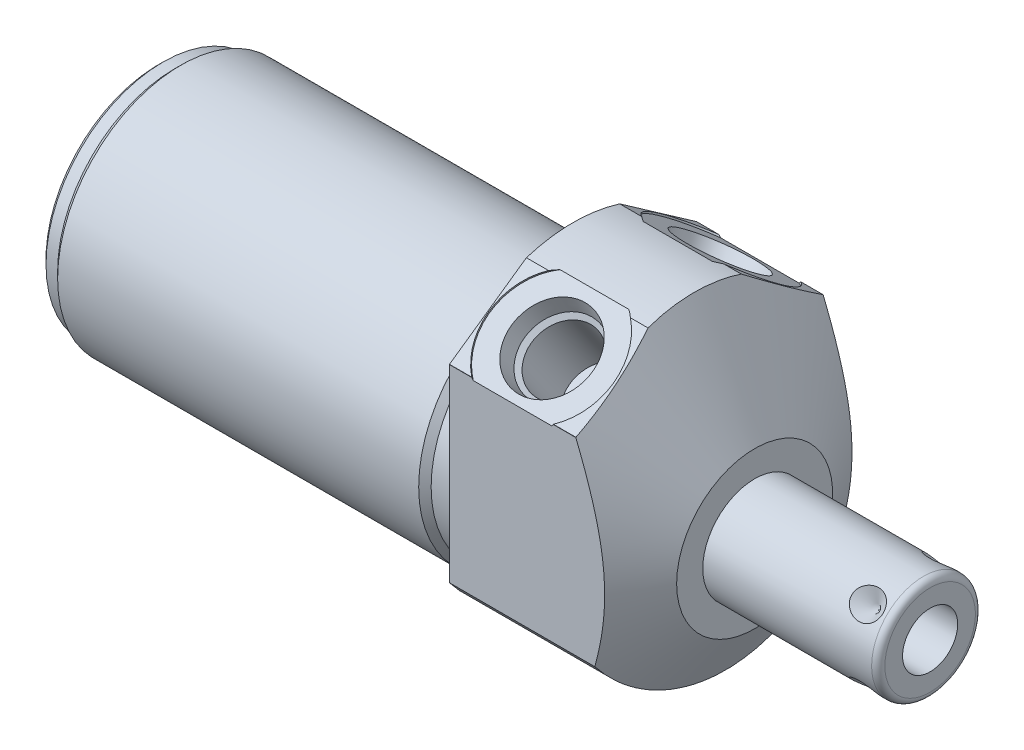
SolidWorks part; units mm, degrees
material "Alloy Steel"
ref_plane "Front Plane" through (0, 0, 0) normal (0, 0, 1) x (1, 0, 0)
ref_plane "Top Plane" through (0, 0, 0) normal (0, 1, 0) x (1, 0, 0)
ref_plane "Right Plane" through (0, 0, 0) normal (1, 0, 0) x (0, 0, -1)
ref_plane "Plane1" through (0, 0, 0) normal (1, 0, 0) x (0, 0, -1)
sketch "Sketch1" plane through (0, 0, 0) normal (1, 0, 0) x (0, 0, -1)
  circle A0 centre (0, 0) radius 23.8125
  dimension "D1" = 47.625
extrude "Extrude1" add sketch "Sketch1" along normal blind 27.7876 and the other way blind 63.5
ref_plane "Plane2" through (0, 0, 0) normal (1, 0, 0) x (0, 0, -1)
sketch "Sketch2" plane through (0, 0, 0) normal (1, 0, 0) x (0, 0, -1)
  line L0 (-20.7455, -4.191) -> (20.7455, -4.191) construction
  circle A0 centre (0, -4.191) radius 18.8595
  circle A1 centre (0, 0) radius 23.8125 construction
  circle A2 centre (0, 0) radius 23.8125
  dimension "D2" = 37.719
  dimension "D1" = 4.191
extrude "Cut-Extrude1" cut sketch "Sketch2" against normal up to next
ref_plane "Plane4" through (0, 0, 0) normal (-1, 0, 0) x (0, 0, 1)
sketch "Sketch4" plane through (0, 0, 0) normal (-1, 0, 0) x (0, 0, 1)
  line L0 (18.923, -14.4553) -> (18.923, 14.4659)
  line L1 (18.923, 14.4659) -> (0, 27.7159)
  line L2 (-18.923, -14.4553) -> (-18.923, 14.4659)
  line L3 (-18.923, 14.4659) -> (0, 27.7159)
  line L4 (0, -26.3889) -> (0, 30.2923) construction
  circle A0 centre (0, 0) radius 28.575
  circle A1 centre (0, 0) radius 23.8125 construction
  arc A3 (-18.923, -14.4553) -> (18.923, -14.4553) centre (0, 0) ccw
  dimension "D4" = 57.15
  dimension "D1" = 37.846
  dimension "D2" = 27.7159
  dimension "D3" = 55
extrude "Cut-Extrude3" cut sketch "Sketch4" against normal up to next
ref_plane "Plane6" through (0, 0, 0) normal (0, 0, 1) x (1, 0, 0)
sketch "Sketch6" plane through (0, 0, 0) normal (0, 0, 1) x (1, 0, 0)
  line L0 (4.764, 47.625) -> (27.7876, 7.747)
  line L1 (3.6128, -4.191) -> (28.9388, -4.191) construction
  line L2 (-63.5, -4.191) -> (0, -4.191) construction
  line L3 (27.7876, 7.747) -> (27.7876, 47.625)
  line L4 (27.7876, 47.625) -> (4.764, 47.625)
  line L5 (27.7876, -14.4553) -> (27.7876, 14.4553) construction
  dimension "D1" = 23.876
  dimension "D2" = 30
  dimension "D3" = 39.878
revolve "Cut-Revolve2" cut sketch "Sketch6" angle 360 about L1
ref_plane "Plane7" through (9.652, 18.3948, 12.869) normal (1, 0, 0) x (0, 0.5736, -0.8192)
sketch "S2D0002" plane through (9.652, 18.3948, 12.869) normal (1, 0, 0) x (0, 0.5736, -0.8192)
  line L0 (0, 0) -> (6.1849, 0)
  line L1 (6.1849, 0) -> (5.6423, -2.5527)
  line L2 (5.6423, -2.5527) -> (4.9784, -3.2166)
  line L3 (4.9784, -3.2166) -> (4.9784, -13.462)
  line L4 (4.9784, -13.462) -> (0, -13.462)
  line L5 (0, -13.462) -> (0, 0)
  line L6 (0, -14.1351) -> (0, 0.6731) construction
  dimension "D1" = 13.462
revolve "Cut-Revolve3" cut sketch "S2D0002" angle 360 about L6
ref_plane "Plane8" through (9.652, 18.3948, -12.869) normal (1, 0, 0) x (0, -0.5736, -0.8192)
sketch "Sketch8" plane through (9.652, 18.3948, -12.869) normal (1, 0, 0) x (0, -0.5736, -0.8192)
  line L0 (0, 0) -> (6.1849, 0)
  line L1 (6.1849, 0) -> (5.6423, -2.5527)
  line L2 (5.6423, -2.5527) -> (4.9784, -3.2166)
  line L3 (4.9784, -3.2166) -> (4.9784, -13.462)
  line L4 (4.9784, -13.462) -> (0, -13.462)
  line L5 (0, -13.462) -> (0, 0)
  line L6 (0, -14.1351) -> (0, 0.6731) construction
  dimension "D1" = 13.462
revolve "Cut-Revolve4" cut sketch "Sketch8" angle 360 about L6
sketch "Sketch18" plane through (0, 18.5976, 13.0222) normal (0, 0.8192, 0.5736) x (1, 0, 0)
  circle A0 centre (9.652, 0.0091) radius 9.525
  dimension "D1" = 19.05
extrude "Cut-Extrude4" cut sketch "Sketch18" against normal blind 0.254
sketch "Sketch19" plane through (0, 18.5976, -13.0222) normal (0, 0.8192, -0.5736) x (1, 0, 0)
  circle A0 centre (9.652, -0.0091) radius 9.525
  dimension "D1" = 19.05
extrude "Cut-Extrude5" cut sketch "Sketch19" against normal blind 0.254
ref_plane "Plane10" through (0, 0, 0) normal (0, 0, 1) x (1, 0, 0)
sketch "Sketch10" plane through (0, 0, 0) normal (0, 0, 1) x (1, 0, 0)
  line L0 (0, 14.6685) -> (0, 13.716)
  line L1 (0, 13.716) -> (-3.81, 13.716)
  line L2 (-3.81, 13.716) -> (-4.7625, 14.6685)
  line L3 (-5.0006, -4.191) -> (0.2381, -4.191) construction
  line L4 (0, 14.6685) -> (-4.7625, 14.6685)
  line L5 (-63.5, -4.191) -> (0, -4.191) construction
  line L6 (0, 14.6685) -> (-63.5, 14.6685) construction
  line L7 (0, 14.6685) -> (0, -23.0505) construction
  dimension "D1" = 35.814
  dimension "D2" = 3.81
  dimension "D3" = 45
revolve "Cut-Revolve6" cut sketch "Sketch10" angle 360 about L3
ref_plane "Plane12" through (0, 0, 0) normal (0, 0, 1) x (1, 0, 0)
sketch "Sketch12" plane through (0, 0, 0) normal (0, 0, 1) x (1, 0, 0)
  line L0 (-63.5, 14.6685) -> (-63.5, 13.716)
  line L1 (-63.5, 13.716) -> (-60.96, 13.716)
  line L2 (-60.96, 13.716) -> (-60.0075, 14.6685)
  line L3 (-63.6746, -4.191) -> (-59.8329, -4.191) construction
  line L4 (-63.5, 14.6685) -> (-60.0075, 14.6685)
  line L6 (-63.5, -4.191) -> (-4.7625, -4.191) construction
  line L7 (-4.7625, 14.6685) -> (-63.5, 14.6685) construction
  line L8 (-63.5, 14.6685) -> (-63.5, -23.0505) construction
  dimension "D1" = 35.814
  dimension "D2" = 2.54
  dimension "D3" = 45
revolve "Cut-Revolve8" cut sketch "Sketch12" angle 360 about L3
chamfer "Chamfer1" distance 0.762 angle 45 1 edges at (-63.5, -4.191, 17.907)
ref_plane "Plane13" through (0, 0, 0) normal (0, 0, 1) x (0, -1, 0)
sketch "Sketch13" plane through (0, 0, 0) normal (0, 0, 1) x (0, -1, 0)
  line L0 (4.191, 27.7876) -> (4.191, 54.6354)
  line L1 (4.191, 54.6354) -> (11.1125, 54.6354)
  line L2 (12.1285, 53.6194) -> (12.1285, 27.7876)
  line L3 (12.1285, 27.7876) -> (4.191, 27.7876)
  line L4 (4.191, 26.4452) -> (4.191, 55.9778) construction
  line L5 (4.191, -60.0075) -> (4.191, -4.7625) construction
  line L6 (16.129, 27.7876) -> (-7.747, 27.7876) construction
  line L7 (14.4553, 0) -> (-14.4553, 0) construction
  arc A0 (12.1285, 53.6194) -> (11.1125, 54.6354) centre (11.1125, 53.6194) ccw
  dimension "D2" = 1.016
  dimension "D1" = 54.6354
  dimension "D3" = 15.875
revolve "Revolve1" add sketch "Sketch13" angle 360 about L4
ref_plane "Plane14" through (54.6354, -8.4074, 0) normal (0, 0, 1) x (0, -1, 0)
sketch "S2D0001" plane through (54.6354, -8.4074, 0) normal (0, 0, 1) x (0, -1, 0)
  line L0 (0, 0) -> (0, -15.24)
  line L1 (0, -15.24) -> (-4.2164, -17.7735)
  line L2 (0, 0) -> (-4.2164, 0)
  line L3 (-4.2164, 0) -> (-4.2164, -17.7735)
  line L4 (-4.2164, -18.6621) -> (-4.2164, 0.8887) construction
  line L5 (-4.2164, -1.016) -> (-4.2164, -26.8478) construction
  line L6 (2.7051, 0) -> (-11.1379, 0) construction
  dimension "D1" = 8.4328
  dimension "D2" = 15.24
  dimension "D3" = 59
revolve "Cut-Revolve9" cut sketch "S2D0001" angle 360 about L4
ref_plane "Plane16" through (50.673, -12.1285, 0) normal (0, 0, 1) x (-1, 0, 0)
ref_plane "Plane17" through (0, -2.0955, -2.0955) normal (0, 0.7071, 0.7071) x (-1, 0, 0)
sketch "Sketch16" plane through (50.673, 1.4217, -5.6127) normal (0, -0.7071, -0.7071) x (-1, 0, 0)
  line L0 (0, 0) -> (2.413, 0)
  line L1 (2.413, 0) -> (0, -2.413)
  line L2 (0, 0) -> (0, -2.413)
  line L3 (0, -5.071) -> (0, 0.1207) construction
  line L4 (-3.9624, -1.016) -> (-3.9624, -14.859) construction
  line L5 (22.8854, 0) -> (-2.9464, 0) construction
  dimension "D1" = 3.9624
  dimension "D2" = 4.826
  dimension "D3" = 45
revolve "Cut-Revolve10" cut sketch "Sketch16" angle 360 about L3
pattern_circular "CirPattern1" count 4 over 360 about axis through (26.4452, -4.191, 0) along (-1, 0, 0) of "Cut-Revolve10"
